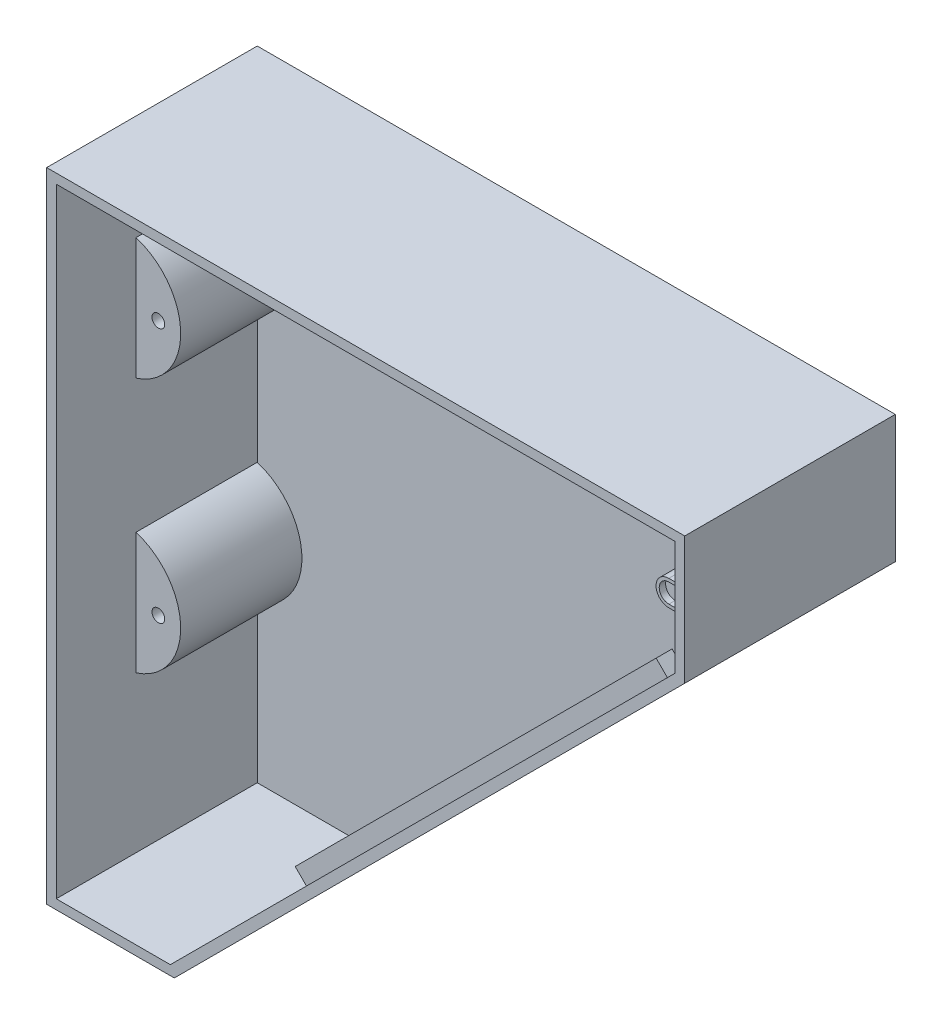
SolidWorks part; units mm, degrees
ref_plane "Piano frontale" through (0, 0, 0) normal (0, 0, 1) x (1, 0, 0)
ref_plane "Piano superiore" through (0, 0, 0) normal (0, 1, 0) x (1, 0, 0)
ref_plane "Piano destro" through (0, 0, 0) normal (1, 0, 0) x (0, 0, -1)
sketch "Schizzo2" plane through (0, 0, 0) normal (0, 0, 1) x (1, 0, 0)
  line L0 (0, 0) -> (0, 200)
  line L1 (0, 200) -> (200, 200)
  line L2 (200, 200) -> (200, 160)
  line L3 (200, 160) -> (40, 0)
  line L4 (40, 0) -> (0, 0)
  dimension "D1" = 45
  dimension "D2" = 40
  dimension "D3" = 200
  dimension "D4" = 200
extrude "Estrusione-Estrusione1" add sketch "Schizzo2" along normal blind 70
shell "Svuota1" thickness 3
sketch "Schizzo5" plane through (200, 0, 0) normal (1, 0, 0) x (0, 0, -1)
  line L0 (-70, 0) -> (0, 0) construction
  line L1 (-70, 200) -> (-66, 200)
  line L2 (-70, 200) -> (-70, 0)
  line L3 (-70, 0) -> (-66, 0)
  line L4 (-66, 200) -> (-66, 0)
  dimension "D1" = 4
extrude "Taglio-Estrusione1" cut sketch "Schizzo5" against normal through all both and the other way through all
ref_plane "Piano1" through (0, 0, 41) normal (0, 0, 1) x (1, 0, 0)
sketch "Schizzo7" plane through (0, 0, 41) normal (0, 0, 1) x (1, 0, 0)
  line L1 (3, 197) -> (3, 3) construction
  line L3 (0, 200) -> (200, 200) construction
  line L4 (3, 170) -> (3, 131.8424)
  line L5 (3, 90) -> (3, 51.8424)
  arc A0 (3, 170) -> (3, 131.8424) centre (-3, 150.9212) cw
  arc A1 (3, 90) -> (3, 51.8424) centre (-3, 70.9212) cw
  dimension "D1" = 20
  dimension "D2" = 6
  dimension "D3" = 30
  dimension "D5" = 80
  dimension "D4" = 2
extrude "Estrusione-Estrusione4" add sketch "Schizzo7" against normal up to vertex (38 mm away) contours A0 L4 | A1 L5
sketch "Schizzo8" plane through (0, 0, 41) normal (0, 0, 1) x (1, 0, 0)
  circle A0 centre (10, 150.9212) radius 2
  arc A1 (3, 131.8424) -> (3, 170) centre (-3, 150.9212) ccw construction
  circle A2 centre (10, 70.9212) radius 2
  point P6 (17, 150.9212)
  dimension "D2" = 4
  dimension "D1" = 13
  dimension "D4" = 80
  dimension "D3" = 2
extrude "Taglio-Estrusione2" cut sketch "Schizzo8" against normal blind 30
ref_plane "Piano2" through (0, 0, 62) normal (0, 0, 1) x (1, 0, 0)
sketch "Schizzo9" plane through (0, 0, 62) normal (0, 0, 1) x (1, 0, 0)
  line L0 (38.7574, 3) -> (197, 161.2426) construction
  line L1 (187, 151.2426) -> (197, 161.2426)
  line L2 (197, 197) -> (197, 161.2426)
  line L3 (187, 197) -> (187, 151.2426)
  line L4 (3, 197) -> (197, 197) construction
  line L5 (187, 197) -> (197, 197)
  dimension "D1" = 10
sketch "Schizzo11" plane through (0, 0, 41) normal (0, 0, 1) x (1, 0, 0)
  line L0 (197, 197) -> (3, 197) construction
  line L1 (28, 197) -> (188, 197)
  line L2 (28, 197) -> (28, 192)
  line L3 (28, 192) -> (188, 192)
  line L4 (188, 197) -> (188, 192)
  line L5 (169.5721, 133.8148) -> (56.435, 20.6777)
  line L6 (38.7574, 3) -> (197, 161.2426) construction
  line L7 (197, 161.2426) -> (38.7574, 3) construction
  line L8 (56.435, 20.6777) -> (52.8995, 24.2132)
  line L9 (52.8995, 24.2132) -> (166.0366, 137.3503)
  line L10 (166.0366, 137.3503) -> (169.5721, 133.8148)
  line L11 (3, 197) -> (3, 170) construction
  dimension "D1" = 5
  dimension "D2" = 160
  dimension "D3" = 25
  dimension "D4" = 25
extrude "Estrusione-Estrusione7" add sketch "Schizzo11" against normal blind 5
sketch "Schizzo12" plane through (0, 0, 62) normal (0, 0, 1) x (1, 0, 0)
  line L1 (200, 200) -> (200, 160) construction
  line L2 (193, 184) -> (197, 184)
  line L3 (197, 197) -> (197, 161.2426) construction
  line L4 (193, 176) -> (197, 176)
  line L5 (197, 184) -> (197, 176)
  arc A0 (193, 184) -> (193, 176) centre (193, 180) ccw
  point P6 (200, 180)
  dimension "D1" = 8
  dimension "D2" = 7
extrude "Estrusione-Estrusione8" add sketch "Schizzo12" against normal up to vertex (62 mm away)
sketch "Schizzo13" plane through (0, 0, 62) normal (0, 0, 1) x (1, 0, 0)
  line L0 (193, 177) -> (196, 177)
  line L3 (193, 176) -> (197, 176)
  line L4 (197, 176) -> (197, 184)
  line L5 (197, 184) -> (193, 184)
  line L6 (193, 176) -> (197, 176)
  line L7 (197, 176) -> (197, 177)
  line L8 (197, 184) -> (193, 184)
  line L9 (196, 177) -> (196, 183) construction
  line L10 (193, 183) -> (197, 183)
  line L11 (196, 177) -> (197, 177)
  line L12 (196, 183) -> (193, 183) construction
  line L13 (197, 183) -> (197, 184)
  line L15 (197, 176) -> (197, 184) construction
  arc A0 (193, 183) -> (193, 177) centre (193, 180) ccw
  arc A1 (193, 184) -> (193, 176) centre (193, 180) ccw
  arc A2 (193, 184) -> (193, 176) centre (193, 180) ccw
  dimension "D1" = 0
  dimension "D2" = 1
extrude "Estrusione-Estrusione9" add sketch "Schizzo13" along normal blind 2
